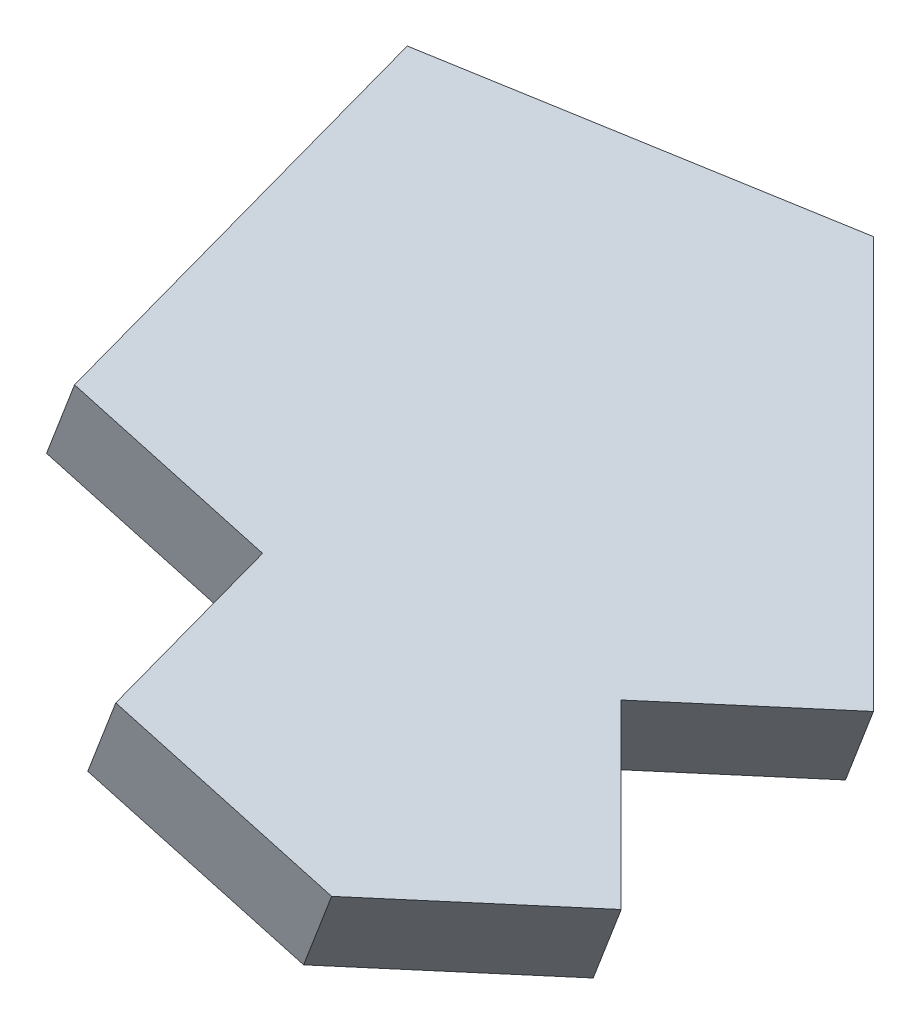
SolidWorks part; units mm, degrees
material "Beech"
ref_plane "Front Plane" through (0, 0, 0) normal (0, 0, 1) x (1, 0, 0)
ref_plane "Top Plane" through (0, 0, 0) normal (0, 1, 0) x (1, 0, 0)
ref_plane "Right Plane" through (0, 0, 0) normal (1, 0, 0) x (0, 0, -1)
sketch "Sketch2" plane through (-12.2675, -19.8492, -7.5817) normal (0.5, 0.809, 0.309) x (0.866, -0.4671, -0.1784)
  line L0 (63.5199, -106.4365) -> (53.907, -106.4365) construction
  line L1 (63.5199, -109.4365) -> (53.907, -109.4365) construction
  line L2 (60.7199, -106.4365) -> (60.7199, -109.4365) construction
  line L3 (72.6849, -102.264) -> (65.5199, -108.6725) construction
  line L4 (65.6069, -104.5698) -> (67.6069, -106.8059) construction
  line L5 (60.7199, -106.4365) -> (57.2829, -106.4365)
  line L6 (63.5199, -109.4365) -> (60.7199, -109.4365)
  line L7 (60.7199, -106.4365) -> (60.7199, -109.4365)
  line L8 (67.6069, -106.8059) -> (65.5199, -108.6725)
  line L9 (65.6069, -104.5698) -> (67.6069, -106.8059)
  line L10 (65.5199, -108.6725) -> (64.6658, -109.4365)
  line L11 (63.5199, -109.4365) -> (64.6658, -109.4365)
  line L12 (64.6658, -109.4365) -> (60.4591, -98.4233) construction
  line L13 (57.2829, -106.4365) -> (57.2829, -99.6365)
  line L14 (68.1686, -102.2785) -> (63.6353, -97.2101)
  line L15 (57.2829, -99.6365) -> (60.4591, -98.4233)
  line L16 (63.6353, -97.2101) -> (60.4591, -98.4233)
  line L17 (65.6069, -104.5698) -> (68.1686, -102.2785)
  dimension "D1" = 90
  dimension "D2" = 6.8
  dimension "D3" = 6.8
extrude "Boss-Extrude1" add sketch "Sketch2" along normal blind 2.8
equation "\"D1@Boss-Extrude1\"=\"T@d20.Assembly\"-0.2"
equation "\"D3@Sketch2\"=\"D2@Sketch2\""
